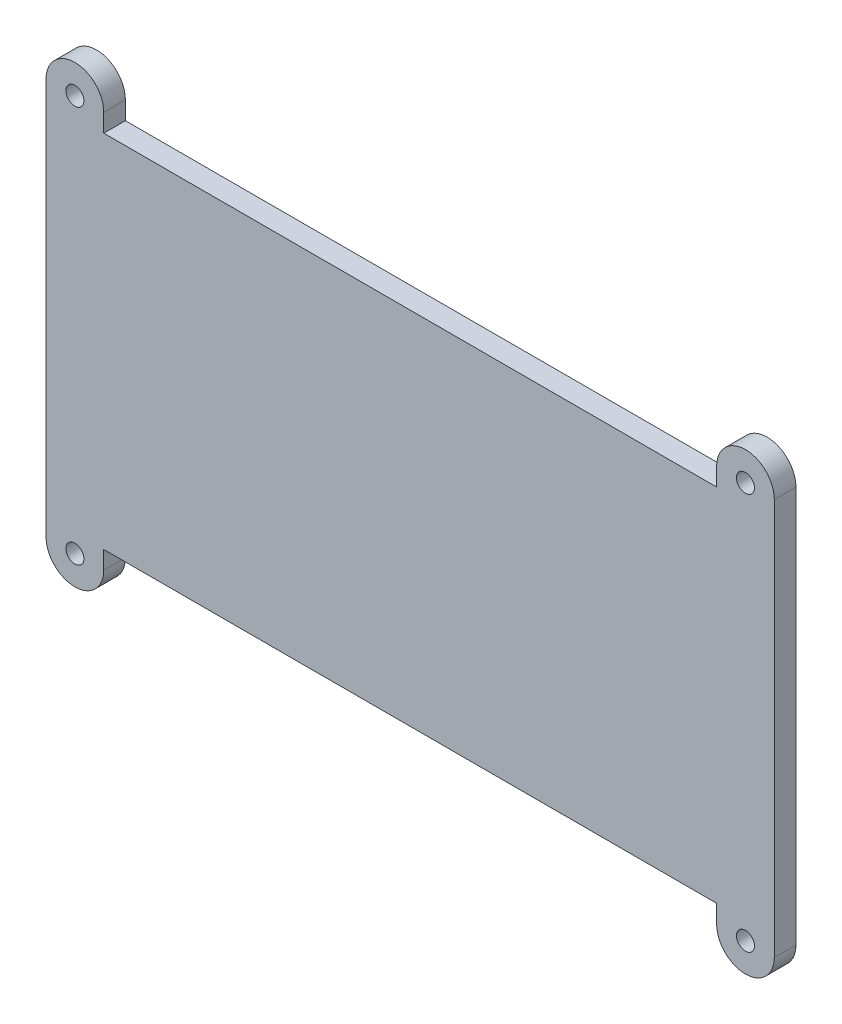
SolidWorks part; units mm, degrees
material "Acrylic (Medium-high impact)"
ref_plane "Front Plane" through (0, 0, 0) normal (0, 0, 1) x (1, 0, 0)
ref_plane "Top Plane" through (0, 0, 0) normal (0, 1, 0) x (1, 0, 0)
ref_plane "Right Plane" through (0, 0, 0) normal (1, 0, 0) x (0, 0, -1)
sketch "Sketch1" plane through (0, 0, 0) normal (0, 0, 1) x (1, 0, 0)
  line L0 (-42.5, -27.5) -> (-42.5, -25)
  line L1 (-46.5, -27.5) -> (46.5, -27.5) construction
  line L2 (-46.5, -27.5) -> (-46.5, 27.5) construction
  line L3 (-46.5, 27.5) -> (46.5, 27.5) construction
  line L4 (46.5, -27.5) -> (46.5, 27.5) construction
  line L5 (-46.5, -27.5) -> (46.5, 27.5) construction
  line L6 (-46.5, 27.5) -> (46.5, -27.5) construction
  line L8 (-50.5, -25) -> (-50.5, 25)
  line L9 (-42.5, 25) -> (42.5, 25)
  line L10 (50.5, -25) -> (50.5, 25)
  line L11 (-50.5, -25) -> (50.5, 25) construction
  line L12 (-50.5, 25) -> (50.5, -25) construction
  line L13 (-50.5, -27.5) -> (-50.5, -25)
  line L14 (-50.5, 27.5) -> (-50.5, 25)
  line L15 (-42.5, 27.5) -> (-42.5, 25)
  line L16 (42.5, 27.5) -> (42.5, 25)
  line L17 (50.5, 27.5) -> (50.5, 25)
  line L18 (50.5, -27.5) -> (50.5, -25)
  line L19 (42.5, -27.5) -> (42.5, -25)
  line L20 (-42.5, -25) -> (42.5, -25)
  circle A0 centre (-46.5, 27.5) radius 1.25
  circle A1 centre (46.5, 27.5) radius 1.25
  circle A2 centre (46.5, -27.5) radius 1.25
  circle A3 centre (-46.5, -27.5) radius 1.25
  arc A5 (50.5, 27.5) -> (42.5, 27.5) centre (46.5, 27.5) ccw
  arc A6 (42.5, -27.5) -> (50.5, -27.5) centre (46.5, -27.5) ccw
  arc A7 (-50.5, -27.5) -> (-42.5, -27.5) centre (-46.5, -27.5) ccw
  arc A8 (-42.5, 27.5) -> (-50.5, 27.5) centre (-46.5, 27.5) ccw
  point P0 (0, 0)
  point P10 (0, 0)
  dimension "D3" = 2.5
  dimension "D1" = 93
  dimension "D2" = 55
  dimension "D4" = 50
  dimension "D5" = 101
extrude "Boss-Extrude1" add sketch "Sketch1" along normal blind 3
